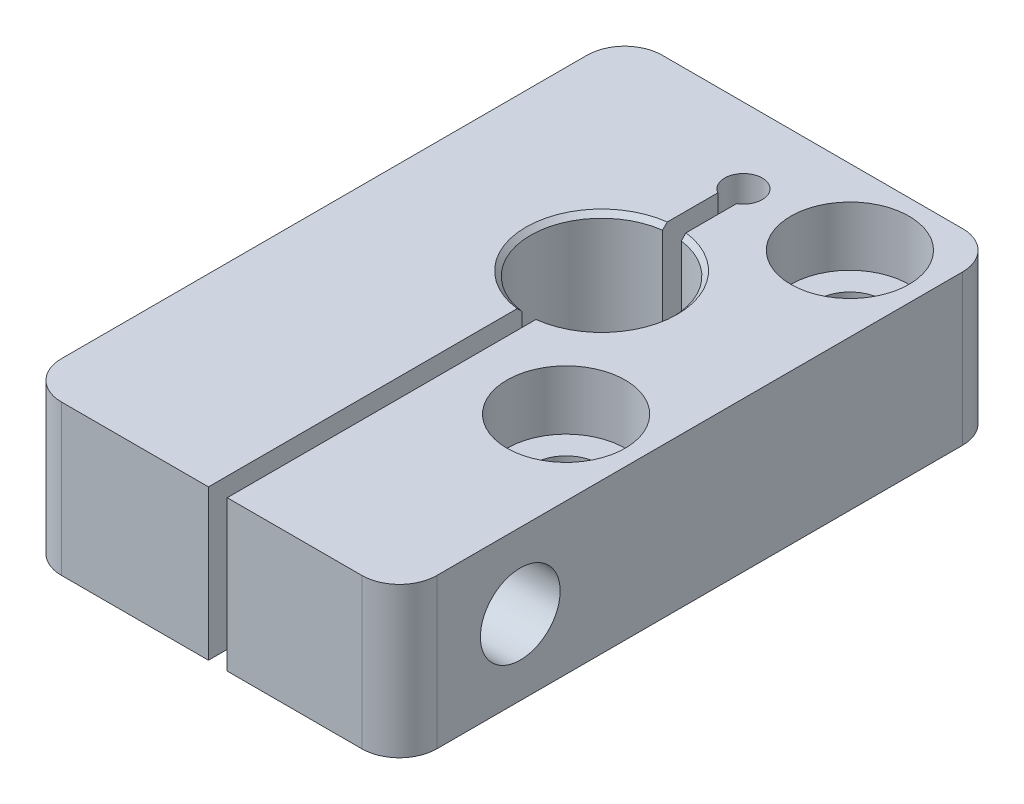
SolidWorks part; units mm, degrees
material "Delrin (Acetal)"
ref_plane "Front Plane" through (0, 0, 0) normal (0, 0, 1) x (1, 0, 0)
ref_plane "Top Plane" through (0, 0, 0) normal (0, 1, 0) x (1, 0, 0)
ref_plane "Right Plane" through (0, 0, 0) normal (1, 0, 0) x (0, 0, -1)
sketch "Sketch1" plane through (0, 0, 0) normal (0, 0, 1) x (0, 1, 0)
  line L1 (-6.35, 15.875) -> (6.35, 15.875)
  line L2 (-6.35, 15.875) -> (-6.35, -15.875)
  line L3 (-6.35, -15.875) -> (6.35, -15.875)
  line L4 (6.35, 15.875) -> (6.35, -15.875)
  line L5 (-6.35, 15.875) -> (6.35, -15.875) construction
  line L6 (-6.35, -15.875) -> (6.35, 15.875) construction
  point P0 (0, 0)
  dimension "Width" = 12.7
  dimension "Height" = 31.75
extrude "Extrude1" add sketch "Sketch1" along normal mid plane 50.8
hole_wizard "CBORE for M5 SHCS1" positions "Sketch2" profile "Sketch3" counterbore size "M5" standard "ANSI Metric" end condition up to next
sketch "Sketch2" plane through (0, 6.35, 0) normal (0, 1, 0) x (-1, 0, 0)
  line L0 (-15.875, -25.4) -> (15.875, -25.4) construction
  line L1 (-15.875, 25.4) -> (-15.875, -25.4) construction
  point P0 (-9.525, -19.05)
  point P2 (-9.525, 4.95)
  dimension "D1" = 24
  dimension "D2" = 6.35
  dimension "D3" = 6.35
sketch "Sketch3" plane through (9.525, 6.35, -19.05) normal (1, 0, 0) x (0, 0, 1)
  line L0 (0, 0) -> (0, 12.7)
  line L1 (0, 12.7) -> (2.75, 12.7)
  line L3 (2.75, 12.7) -> (2.75, 5)
  line L4 (2.75, 5) -> (5, 5)
  line L5 (5, 5) -> (5, 0)
  line L7 (5, 0) -> (0, 0)
  line L11 (0, -6.35) -> (0, 107.95) construction
  dimension "Thru Hole Dia." = 5.5
  dimension "Thru Hole Depth" = 12.7
  dimension "C'Bore Dia." = 10
  dimension "C'Bore Depth" = 5
sketch "Sketch4" plane through (0, 6.35, 0) normal (0, 1, 0) x (1, 0, 0)
  line L0 (15.875, -25.4) -> (-15.875, -25.4) construction
  line L2 (-0.2687, 17.6752) -> (-0.2687, 12.9973)
  line L3 (-0.2687, -25.4) -> (1.3188, -25.4)
  line L4 (1.3188, 17.6752) -> (1.3188, 12.9973)
  line L5 (-0.2687, 1.1027) -> (-0.2687, -25.4)
  line L6 (1.3188, 1.1027) -> (1.3188, -25.4)
  line L7 (0.525, 7.05) -> (9.525, -4.95) construction
  line L8 (9.525, 19.05) -> (9.525, -4.95) construction
  line L9 (0.525, 7.05) -> (9.525, 7.05) construction
  arc A0 (1.3188, 1.1027) -> (1.3188, 12.9973) centre (0.525, 7.05) ccw
  arc A1 (1.3188, 17.6752) -> (-0.2687, 17.6752) centre (0.525, 19.05) ccw
  arc A2 (-0.2687, 12.9973) -> (-0.2687, 1.1027) centre (0.525, 7.05) ccw
  dimension "D3" = 6
  dimension "D5" = 1.5875
  dimension "D1" = 1.5875
  dimension "D4" = 15
extrude "Cut-Extrude1" cut sketch "Sketch4" against normal up to next
hole_wizard "17/64 (0.26563) Diameter Hole1" positions "Sketch5" profile "Sketch6" hole size "17/64" standard "ANSI Inch" end condition up to next
sketch "Sketch5" plane through (15.875, 0, 0) normal (1, 0, 0) x (0, 0, -1)
  line L0 (7.05, -6.35) -> (7.05, 6.35) construction
  point P0 (-15.175, 0)
  dimension "D1" = 22.225
sketch "Sketch6" plane through (15.875, 0, 15.175) normal (0, 1, 0) x (0, 0, -1)
  line L0 (0, 0) -> (0, 14.5562)
  line L1 (0, 14.5562) -> (3.3735, 14.5562)
  line L2 (3.3735, 14.5562) -> (3.3735, 0)
  line L5 (3.3735, 0) -> (0, 0)
  line L11 (0, -6.35) -> (0, 107.95) construction
  dimension "Thru Hole Dia." = 6.747
  dimension "Thru Hole Depth" = 14.5562
hole_wizard "M6x1.0 Tapped Hole1" positions "Sketch7" profile "Sketch8" tap size "M6x1.0" standard "ANSI Metric" end condition up to next
sketch "Sketch7" plane through (-0.2687, 0, 0) normal (1, 0, 0) x (0, 0, -1)
  point P0 (-15.175, 0)
sketch "Sketch8" plane through (-0.2687, 0, 15.175) normal (0, 1, 0) x (0, 0, -1)
  line L0 (0, 0) -> (0, 15.6063)
  line L1 (0, 15.6063) -> (2.5, 15.6063)
  line L2 (2.5, 15.6063) -> (2.5, 0)
  line L5 (2.5, 0) -> (0, 0)
  line L11 (0, -6.35) -> (0, 107.95) construction
  dimension "Thru Tap Drill Dia." = 5
  dimension "Thru Tap Drill Depth" = 15.6063
cosmetic thread "Hole Thread1" parameters "D2"=6
fillet "Fillet1" radius 3.175 4 edges at (-15.875, 0, -25.4) (15.875, 0, -25.4) (15.875, 0, 25.4) (-15.875, 0, 25.4)
chamfer "Chamfer1" distance 0.3969 angle 45 4 edges at (6.525, 6.35, -7.05) (-5.475, 6.35, -7.05) (6.525, -6.35, -7.05) (-5.475, -6.35, -7.05)
sketch "Sketch9" plane through (0, 6.35, 0) normal (0, 1, 0) x (1, 0, 0)
  line L0 (-15.875, -22.225) -> (-15.875, 22.225) construction
  line L1 (-15.875, -20.6375) -> (15.875, -20.6375)
  line L2 (-15.875, -20.6375) -> (-15.875, -25.4)
  line L3 (-15.875, -25.4) -> (15.875, -25.4)
  line L4 (15.875, -20.6375) -> (15.875, -25.4)
  line L5 (12.7, -25.4) -> (1.3188, -25.4) construction
  line L6 (15.875, -22.225) -> (15.875, 22.225) construction
  dimension "D1" = 4.7625
extrude "Cut-Extrude2" [suppressed] cut sketch "Sketch9" against normal through all
